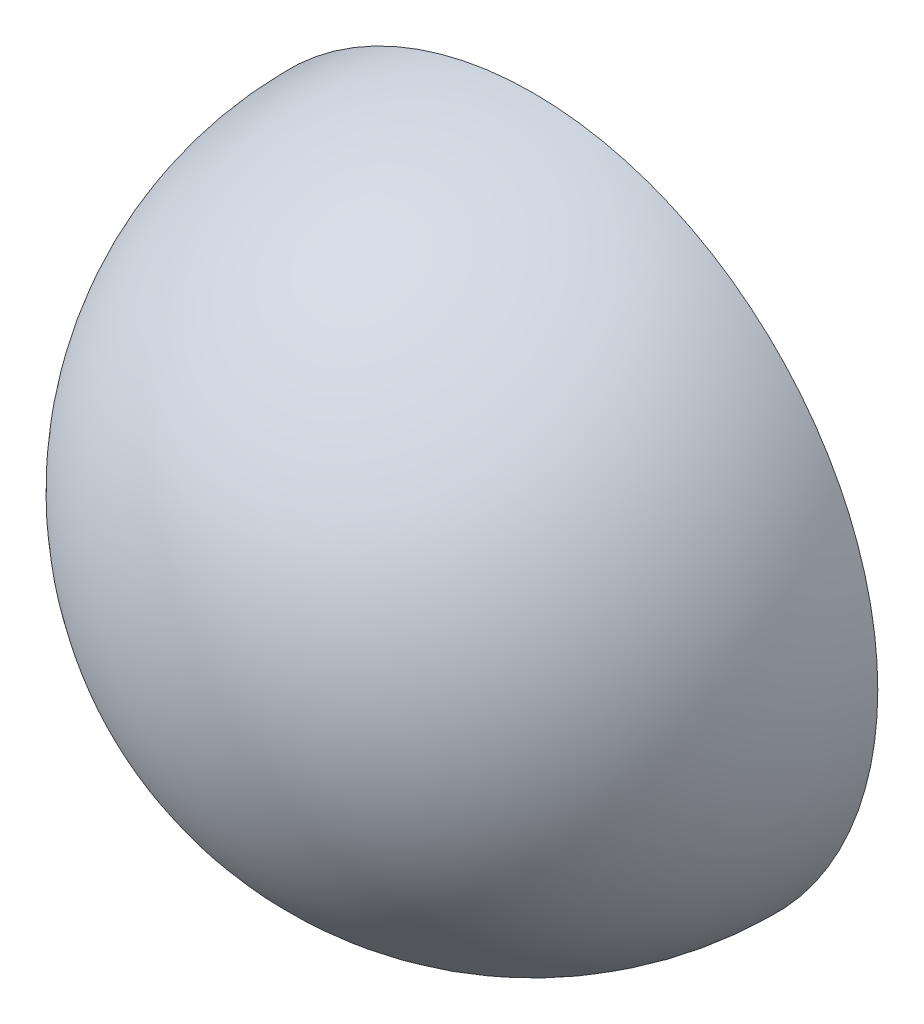
SolidWorks part; units mm, degrees
ref_plane "Front Plane" through (0, 0, 0) normal (0, 0, 1) x (1, 0, 0)
ref_plane "Top Plane" through (0, 0, 0) normal (0, 1, 0) x (1, 0, 0)
ref_plane "Right Plane" through (0, 0, 0) normal (1, 0, 0) x (0, 0, -1)
sketch "Sketch1" plane through (0, 0, 0) normal (0, 1, 0) x (1, 0, 0)
  line L0 (0, 0) -> (18.6879, 0) construction
  line L1 (0, 0) -> (0, -14.4281) construction
  line L2 (-1.25, 0) -> (0, 0)
  line L3 (0, -1.25) -> (0, 0)
  arc A0 (-1.25, 0) -> (0, -1.25) centre (0, 0) ccw
  dimension "D1" = 1.25
  dimension "D2" = 1.25
revolve "Revolve1" add sketch "Sketch1" angle 360 about L3
